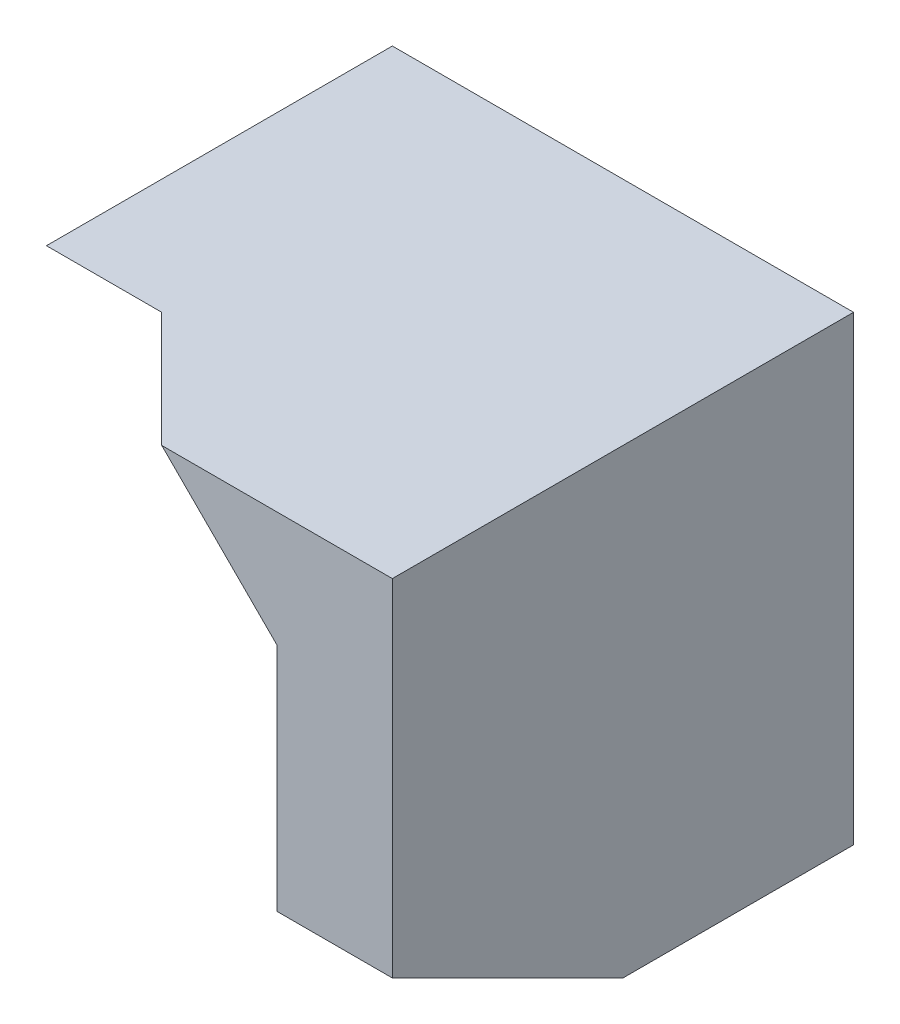
SolidWorks part; units mm, degrees
ref_plane "Front Plane" through (0, 0, 0) normal (0, 0, 1) x (1, 0, 0)
ref_plane "Top Plane" through (0, 0, 0) normal (0, 1, 0) x (1, 0, 0)
ref_plane "Right Plane" through (0, 0, 0) normal (1, 0, 0) x (0, 0, -1)
sketch "Sketch1" plane through (0, 0, 0) normal (0, 0, 1) x (1, 0, 0)
  line L1 (0, 0) -> (40, 0)
  line L2 (0, 0) -> (0, 40)
  line L3 (0, 40) -> (40, 40)
  line L4 (40, 0) -> (40, 40)
  dimension "D1" = 40
  dimension "D2" = 40
extrude "Boss-Extrude1" add sketch "Sketch1" along normal blind 20
sketch "Sketch2" plane through (0, 0, 20) normal (0, 0, 1) x (1, 0, 0)
  line L0 (40, 0) -> (30, 0)
  line L1 (0, 0) -> (40, 0) construction
  line L2 (30, 0) -> (10, 20)
  line L3 (10, 20) -> (0, 20)
  line L4 (0, 40) -> (0, 0) construction
  line L5 (0, 20) -> (0, 40)
  line L6 (0, 20) -> (0, 0)
  line L7 (0, 0) -> (30, 0)
  line M5 (0, 40) -> (0, 0)
  line M6 (0, 0) -> (40, 0)
  dimension "D1" = 20
  dimension "D2" = 10
  dimension "D3" = 10
extrude "Cut-Extrude1" cut sketch "Sketch2" against normal blind 20 contours L2 L3 M5 M6
sketch "Sketch3" plane through (0, 0, 0) normal (-1, 0, 0) x (0, 0, 1)
  line L1 (20, 20) -> (10, 20)
  line L2 (20, 20) -> (20, 30)
  line L3 (20, 30) -> (10, 30)
  line L4 (10, 20) -> (10, 30)
  dimension "D1" = 10
  dimension "D2" = 10
extrude "Cut-Extrude2" cut sketch "Sketch3" against normal blind 10
sketch "Sketch5" plane through (40, 0, 0) normal (1, 0, 0) x (0, 0, -1)
  line L0 (-20, 40) -> (-20, 0)
  line L1 (-20, 40) -> (-40, 40)
  line L2 (-40, 40) -> (-40, 10)
  line L3 (-40, 10) -> (-20, 0)
  dimension "D1" = 20
  dimension "D2" = 10
extrude "Boss-Extrude2" add sketch "Sketch5" against normal blind 10
sketch "Sketch7" plane through (0, 0, 40) normal (0, 0, 1) x (1, 0, 0)
  line L0 (30, 30) -> (30, 40)
  line L1 (30, 40) -> (30, 10) construction
  line L2 (30, 40) -> (20, 40)
  line L3 (20, 40) -> (30, 30)
  dimension "D1" = 10
  dimension "D2" = 10
extrude "Boss-Extrude3" add sketch "Sketch7" against normal blind 29
sketch "Sketch8" plane through (0, 0, 0) normal (-1, 0, 0) x (0, 0, 1)
  line L0 (20, 40) -> (20, 30)
  line L1 (20, 40) -> (30, 40)
  line L2 (30, 40) -> (20, 30)
  dimension "D1" = 10
extrude "Boss-Extrude4" add sketch "Sketch8" against normal blind 10
sketch "Sketch9" plane through (0, 0, 20) normal (0, 0, 1) x (1, 0, 0)
  line L0 (10, 30) -> (20, 20)
  line L1 (20, 20) -> (20, 10)
  line L2 (30, 0) -> (10, 20) construction
  line L3 (10, 30) -> (10, 20)
  line L4 (10, 20) -> (20, 10)
  dimension "D1" = 10
  dimension "D2" = 10
extrude "Cut-Extrude3" cut sketch "Sketch9" against normal blind 10
sketch "Sketch10" plane through (0, 0, 20) normal (0, 0, 1) x (1, 0, 0)
  line L0 (20, 20) -> (30, 10)
  line L1 (30, 0) -> (30, 30) construction
  dimension "D1" = 10
sketch "Sketch11" plane through (30, 0, 0) normal (-1, 0, 0) x (0, 0, 1)
  line L0 (40, 30) -> (20, 10)
sketch "Sketch12" plane through (0, 40, 0) normal (0, 1, 0) x (1, 0, 0)
  line L0 (20, -40) -> (10, -30)
  line L1 (10, -30) -> (0, -30) construction
sketch "Sketch13" plane through (10, 0, 0) normal (1, 0, 0) x (0, 0, -1)
  line L0 (-30, 40) -> (-20, 30)
sketch "Sketch14" plane through (0, 0, 20) normal (0, 0, 1) x (1, 0, 0)
  line L0 (20, 20) -> (10, 30)
  line L8 (10, 40) -> (10, 30)
  line L9 (10, 30) -> (20, 20)
  line L10 (20, 20) -> (20, 10)
  line L11 (20, 10) -> (30, 0)
  line L12 (30, 0) -> (30, 30)
  line L13 (30, 30) -> (20, 40)
  line L14 (20, 40) -> (10, 40)
  line L15 (10, 40) -> (10, 30)
  line L17 (20, 20) -> (20, 10)
  line L18 (20, 10) -> (30, 0)
  line L19 (30, 0) -> (30, 30)
  line L20 (30, 30) -> (20, 40)
  line L21 (20, 40) -> (10, 40)
  dimension "D1" = 0
ref_plane "Plane1" through (6.6667, 6.6667, -6.6667) normal (0.5774, 0.5774, -0.5774) x (-0.4082, -0.4082, -0.8165)
sketch "Sketch15" plane through (6.6667, 6.6667, -6.6667) normal (0.5774, 0.5774, -0.5774) x (-0.4082, -0.4082, -0.8165)
  line L0 (-57.1548, 0) -> (-57.1548, 14.1421)
  line L1 (-57.1548, 14.1421) -> (-32.6599, 14.1421)
  line L2 (-32.6599, 14.1421) -> (-32.6599, -14.1421)
  line L3 (-32.6599, -14.1421) -> (-57.1548, 0)
extrude "Boss-Extrude5" add sketch "Sketch15" along normal blind 10
sketch "Sketch17" plane through (0, 0, 0) normal (-1, 0, 0) x (0, 0, 1)
  line L1 (20, 30) -> (30, 30)
  line L2 (20, 30) -> (20, 40)
  line L3 (20, 40) -> (30, 40)
  line L4 (30, 30) -> (30, 40)
extrude "Boss-Extrude8" add sketch "Sketch17" against normal blind 30
sketch "Sketch18" plane through (0, 40, 0) normal (0, 1, 0) x (1, 0, 0)
  line L0 (20, -40) -> (31.547, -34.2265)
  line L1 (20, -40) -> (31.547, -34.2265) construction
  line L2 (31.547, -34.2265) -> (20, -22.6795)
  line L3 (20, -22.6795) -> (20, -30)
  line L4 (20, -30) -> (20, -40)
extrude "Cut-Extrude4" cut sketch "Sketch18" along normal blind 30
sketch "Sketch19" plane through (0, 0, 0) normal (-1, 0, 0) x (0, 0, 1)
  line L0 (30, 40) -> (20, 30)
  line L1 (30, 30) -> (10, 30) construction
  line L2 (20, 30) -> (30, 30)
  line L3 (30, 30) -> (30, 40)
  dimension "D1" = 10
extrude "Cut-Extrude5" cut sketch "Sketch19" against normal blind 10
sketch "Sketch20" plane through (6.6667, 6.6667, -6.6667) normal (-0.5774, -0.5774, 0.5774) x (0.4082, 0.4082, 0.8165)
  line L0 (44.9073, 7.0711) -> (44.9073, 14.1421)
  line L1 (44.9073, 14.1421) -> (32.6599, 14.1421)
  line L2 (32.6599, 14.1421) -> (44.9073, 7.0711)
extrude "Cut-Extrude6" cut sketch "Sketch20" along normal blind 10
sketch "Sketch21" plane through (0, 40, 0) normal (0, 1, 0) x (1, 0, 0)
  line L1 (20, -30) -> (15, -30)
  line L2 (20, -30) -> (20, -40)
  line L3 (20, -40) -> (15, -40)
  line L4 (15, -30) -> (15, -40)
  dimension "D1" = 5
  dimension "D2" = 10
extrude "Boss-Extrude9" add sketch "Sketch21" against normal blind 5
sketch "Sketch22" plane through (0, 40, 0) normal (0, 1, 0) x (1, 0, 0)
  line L0 (20, -40) -> (15, -35)
  line L1 (15, -30) -> (15, -40) construction
  line L2 (15, -35) -> (15, -40)
  line L3 (15, -40) -> (20, -40)
extrude "Cut-Extrude7" cut sketch "Sketch22" against normal blind 5
sketch "Sketch23" plane through (6.6667, 6.6667, -6.6667) normal (-0.5774, -0.5774, 0.5774) x (0.4082, 0.4082, 0.8165)
  line L0 (44.9073, 14.1421) -> (44.9073, 21.2132)
  line L1 (44.9073, 21.2132) -> (32.6599, 14.1421)
  line L2 (32.6599, 14.1421) -> (44.9073, 14.1421)
extrude "Cut-Extrude8" cut sketch "Sketch23" along normal blind 5
sketch "Sketch24" plane through (3.7799, 3.7799, -3.7799) normal (0.5774, 0.5774, -0.5774) x (-0.4082, -0.4082, -0.8165)
  line L0 (-41.3718, 14.1421) -> (-41.3718, 15.0895)
  line L1 (-41.3718, 15.0895) -> (-39.7309, 14.1421)
  line L2 (-39.7309, 14.1421) -> (-41.3718, 14.1421)
extrude "Cut-Extrude9" cut sketch "Sketch24" against normal blind 5
sketch "Sketch25" plane through (0, 40, 0) normal (0, 1, 0) x (1, 0, 0)
  line L0 (15, -35) -> (10, -30)
  line L1 (10, -30) -> (15, -30)
  line L2 (15, -30) -> (15, -35)
extrude "Boss-Extrude10" add sketch "Sketch25" against normal blind 5
sketch "Sketch26" plane through (0, 0, 30) normal (0, 0, -1) x (-1, 0, 0)
  line L0 (-15, 35) -> (-10, 40)
  line L1 (-10, 40) -> (-10, 35)
  line L2 (-10, 35) -> (-15, 35)
extrude "Boss-Extrude11" add sketch "Sketch26" along normal blind 5
sketch "Sketch27" plane through (0, 0, 0) normal (0, 0, -1) x (-1, 0, 0)
  line L0 (-40, 40) -> (0, 40) construction
  line L1 (-40, 40) -> (-20, 40)
  line L2 (-40, 40) -> (-40, 35)
  line L3 (-40, 35) -> (-20, 35)
  line L4 (-20, 40) -> (-20, 35)
  line L5 (-40, 0) -> (-40, 40) construction
  dimension "D1" = 20
  dimension "D2" = 5
  dimension "D3" = 0
extrude "Boss-Extrude12" add sketch "Sketch27" against normal blind 40
sketch3d "3DSketch1"
  line L0 (10, 30, 20) -> (10, 40, 30)
  line L1 (10, 40, 30) -> (20, 40, 40)
  line L2 (20, 40, 40) -> (30, 30, 40)
  line L3 (30, 30, 40) -> (30, 10, 20)
  line L4 (30, 10, 20) -> (10, 30, 20)
extrude "Cut-Extrude10" cut sketch "3DSketch1" along direction (0, 0, 1) on the side against the normal blind 19
